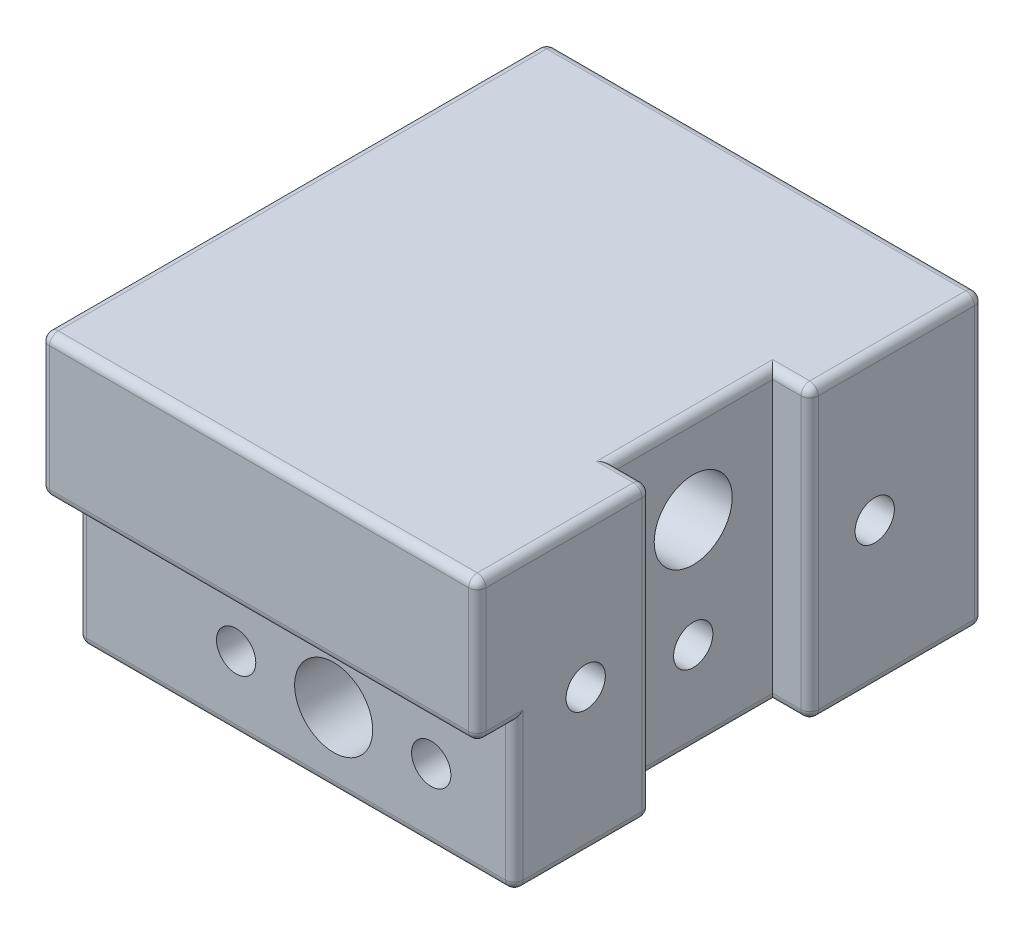
SolidWorks part; units mm, degrees
ref_plane "Front Plane" through (0, 0, 0) normal (0, 0, 1) x (1, 0, 0)
ref_plane "Top Plane" through (0, 0, 0) normal (0, 1, 0) x (1, 0, 0)
ref_plane "Right Plane" through (0, 0, 0) normal (1, 0, 0) x (0, 0, -1)
sketch "Sketch1" plane through (0, 0, 0) normal (0, 1, 0) x (1, 0, 0)
  line L1 (0, 44.45) -> (38.354, 44.45)
  line L2 (0, 44.45) -> (0, 0)
  line L3 (0, 0) -> (38.354, 0)
  line L4 (38.354, 44.45) -> (38.354, 0)
  dimension "D1" = 38.354
  dimension "D2" = 44.45
extrude "Boss-Extrude1" add sketch "Sketch1" along normal blind 25.4
sketch "Sketch2" plane through (0, 0, 0) normal (0, 0, 1) x (1, 0, 0)
  line L0 (22.479, 6.35) -> (22.479, 0) construction
  line L1 (0, 0) -> (38.354, 0) construction
  line L2 (38.354, 25.4) -> (38.354, 0) construction
  circle A0 centre (22.479, 6.35) radius 3.429
  dimension "D3" = 6.858
  dimension "D1" = 15.875
  dimension "D2" = 6.35
extrude "Cut-Extrude1" cut sketch "Sketch2" against normal up to surface (44.45 mm away) up to face at (19.177, 12.7, -44.45)
sketch "Sketch3" plane through (38.354, 0, 0) normal (1, 0, 0) x (0, 0, -1)
  line L0 (22.225, 25.4) -> (22.225, 0) construction
  line L1 (9.525, 12.7) -> (34.925, 12.7) construction
  line L2 (0, 25.4) -> (44.45, 25.4) construction
  line L3 (0, 0) -> (44.45, 0) construction
  circle A0 centre (9.525, 12.7) radius 1.7272
  circle A1 centre (34.925, 12.7) radius 1.7272
  point P8 (22.225, 12.7)
  dimension "D2" = 3.4544
  dimension "D1" = 25.4
extrude "Cut-Extrude2" cut sketch "Sketch3" against normal blind 12.7
sketch "Sketch5" plane through (0, 0, 0) normal (-1, 0, 0) x (0, 0, 1)
  line L0 (-22.225, 6.35) -> (-22.225, 0) construction
  line L1 (-31.75, 6.35) -> (-12.7, 6.35) construction
  line L3 (-44.45, 0) -> (0, 0) construction
  circle A0 centre (-31.75, 6.35) radius 1.7272
  circle A1 centre (-12.7, 6.35) radius 1.7272
  dimension "D2" = 3.4544
  dimension "D1" = 19.05
  dimension "D3" = 6.35
extrude "Cut-Extrude4" cut sketch "Sketch5" against normal blind 12.7
sketch "Sketch6" plane through (0, 0, 0) normal (-1, 0, 0) x (0, 0, 1)
  line L0 (-22.225, 17.4625) -> (-22.225, 0) construction
  line L1 (-44.45, 0) -> (0, 0) construction
  circle A0 centre (-22.225, 17.4625) radius 3.429
  dimension "D2" = 6.858
  dimension "D1" = 17.4625
extrude "Cut-Extrude5" cut sketch "Sketch6" against normal up to surface (38.354 mm away) up to face at (38.354, 12.7, -11.2522)
sketch "Sketch7" plane through (0, 0, -44.45) normal (0, 0, -1) x (-1, 0, 0)
  line L0 (-31.0515, 6.35) -> (-13.9065, 6.35) construction
  line L1 (-38.354, 0) -> (0, 0) construction
  circle A0 centre (-31.0515, 6.35) radius 1.7272
  circle A1 centre (-13.9065, 6.35) radius 1.7272
  dimension "D2" = 3.4544
  dimension "D1" = 17.145
extrude "Cut-Extrude6" cut sketch "Sketch7" against normal blind 9.525
sketch "Sketch11" plane through (0, 0, 0) normal (0, 0, 1) x (1, 0, 0)
  line L0 (0, 25.4) -> (0, 0) construction
  line L1 (0, 12.954) -> (38.354, 12.954)
  line L2 (0, 12.954) -> (0, 0)
  line L3 (0, 0) -> (38.354, 0)
  line L4 (38.354, 12.954) -> (38.354, 0)
  line L5 (38.354, 25.4) -> (38.354, 0) construction
  dimension "D1" = 12.954
extrude "Cut-Extrude9" cut sketch "Sketch11" against normal blind 3.2512
sketch "Sketch8" plane through (0, 0, -3.2512) normal (0, 0, 1) x (1, 0, 0)
  circle A1 centre (13.9065, 6.35) radius 1.7272
  circle A2 centre (31.0515, 6.35) radius 1.7272
  circle A3 centre (13.9065, 6.35) radius 1.7272 construction
  circle A4 centre (31.0515, 6.35) radius 1.7272 construction
extrude "Cut-Extrude7" cut sketch "Sketch8" against normal blind 7.62
sketch "Sketch9" plane through (0, 0, -44.45) normal (0, 0, -1) x (-1, 0, 0)
  line L0 (-32.5451, 0) -> (-12.4129, 0)
  line L1 (-38.354, 0) -> (0, 0) construction
  arc A0 (-32.5451, 0) -> (-12.4129, 0) centre (-22.479, 6.35) cw
  circle A1 centre (-22.479, 6.35) radius 3.429 construction
  circle A2 centre (-31.0515, 6.35) radius 1.7272
  circle A3 centre (-13.9065, 6.35) radius 1.7272
  circle A4 centre (-31.0515, 6.35) radius 1.7272 construction
  circle A5 centre (-13.9065, 6.35) radius 1.7272 construction
  circle A6 centre (-22.479, 6.35) radius 3.429
  dimension "D1" = 11.9016
extrude "Boss-Extrude2" add sketch "Sketch9" along normal blind 2.54
sketch "Sketch12" plane through (38.354, 0, 0) normal (1, 0, 0) x (0, 0, -1)
  line L0 (22.225, 25.4) -> (22.225, 17.4625) construction
  line L1 (15.24, 25.4) -> (29.21, 25.4)
  line L2 (15.24, 25.4) -> (15.24, 0)
  line L3 (15.24, 0) -> (29.21, 0)
  line L4 (29.21, 25.4) -> (29.21, 0)
  line L5 (0, 25.4) -> (44.45, 25.4) construction
  line L6 (3.2512, 0) -> (44.45, 0) construction
  circle A0 centre (22.225, 17.4625) radius 3.429 construction
  dimension "D1" = 13.97
extrude "Cut-Extrude10" cut sketch "Sketch12" against normal blind 3.2512
sketch "Sketch13" plane through (35.1028, 0, 0) normal (1, 0, 0) x (0, 0, -1)
  line L0 (22.225, 17.4625) -> (22.225, 7.9375) construction
  line L1 (15.24, 0) -> (29.21, 0) construction
  circle A0 centre (22.225, 17.4625) radius 3.429 construction
  circle A1 centre (22.225, 7.9375) radius 1.7272
  dimension "D1" = 3.4544
  dimension "D2" = 9.525
extrude "Cut-Extrude11" cut sketch "Sketch13" against normal blind 6.35
fillet "Fillet1" radius 0.762 30 edges at (0, 6.477, -3.2512) (0, 12.954, -1.6256) (0, 19.177, 0) (0, 12.7, -44.45) (35.4495, 0, -44.45) (6.2065, 0, -44.45) (19.177, 25.4, 0) (19.177, 25.4, -44.45) (38.354, 12.7, -44.45) (38.354, 25.4, -36.83) (38.354, 0, -36.83) (38.354, 12.7, -29.21) (38.354, 25.4, -7.62) (38.354, 12.7, -15.24) (38.354, 0, -9.2456) (38.354, 6.477, -3.2512) (38.354, 12.954, -1.6256) (38.354, 19.177, 0) (19.177, 12.954, 0) (19.177, 0, -3.2512) (0, 0, -23.8506) (0, 25.4, -22.225) (32.5451, 0, -45.72) (12.4129, 0, -45.72) (36.7284, 25.4, -29.21) (35.1028, 25.4, -22.225) (36.7284, 25.4, -15.24) (36.7284, 0, -29.21) (35.1028, 0, -22.225) (36.7284, 0, -15.24)
